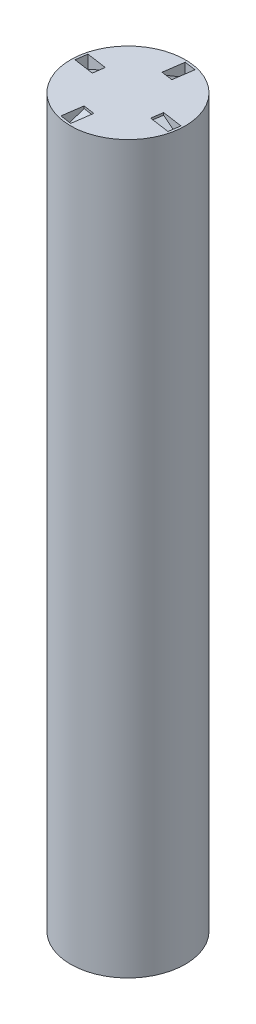
SolidWorks part; units mm, degrees
ref_plane "Front Plane" through (0, 0, 0) normal (0, 0, 1) x (1, 0, 0)
ref_plane "Top Plane" through (0, 0, 0) normal (0, 1, 0) x (1, 0, 0)
ref_plane "Right Plane" through (0, 0, 0) normal (1, 0, 0) x (0, 0, -1)
sketch "Sketch1" plane through (0, 0, 0) normal (0, 1, 0) x (1, 0, 0)
  circle A0 centre (0, 0) radius 6.395
  dimension "D1" = 12.79
extrude "Boss-Extrude1" add sketch "Sketch1" along normal blind 80.99
sketch "Sketch2" [suppressed] plane through (0, 0, 0) normal (0, -1, 0) x (1, 0, 0)
  line L1 (-3.07, -1.85) -> (3.07, -1.85)
  line L2 (-3.07, -1.85) -> (-3.07, 1.85)
  line L3 (-3.07, 1.85) -> (3.07, 1.85)
  line L4 (3.07, -1.85) -> (3.07, 1.85)
  line L5 (-3.07, -1.85) -> (3.07, 1.85) construction
  line L6 (-3.07, 1.85) -> (3.07, -1.85) construction
  point P0 (0, 0)
  dimension "D1" = 6.14
  dimension "D2" = 3.7
sketch "Sketch3" plane through (0, 0, 0) normal (0, -1, 0) x (1, 0, 0)
  line L1 (-3.07, -1.85) -> (3.07, -1.85)
  line L2 (-3.07, -1.85) -> (-3.07, 1.85)
  line L3 (-3.07, 1.85) -> (3.07, 1.85)
  line L4 (3.07, -1.85) -> (3.07, 1.85)
  line L5 (-3.07, -1.85) -> (3.07, 1.85) construction
  line L6 (-3.07, 1.85) -> (3.07, -1.85) construction
  point P0 (0, 0)
  dimension "D1" = 6.14
  dimension "D2" = 3.7
extrude "Cut-Extrude2" cut sketch "Sketch3" against normal blind 8.5
sketch "Sketch4" plane through (-0.0913, 0, 0.6335) normal (-0.1426, 0, 0.9898) x (0.9898, 0, 0.1426)
  line L0 (-3.841, 80.99) -> (-6.121, 80.99)
  line L1 (6.395, 80.99) -> (-6.395, 80.99) construction
  line L2 (-3.841, 80.7337) -> (-3.841, 81.9237) construction
  line L3 (-6.121, 79.5137) -> (-6.121, 81.9237) construction
  line L4 (-6.121, 80.99) -> (-6.121, 79.5137)
  line L5 (-6.121, 79.5137) -> (-3.841, 80.7337)
  line L6 (-3.841, 80.7337) -> (-3.841, 80.99)
  dimension "D1" = 0.2563
  dimension "D2" = 2.28
  dimension "D3" = 1.4763
extrude "Cut-Extrude3" cut sketch "Sketch4" against normal blind 1.28
pattern_circular "CirPattern1" count 4 over 360 about axis through (0, 0, 0) along (0, 1, 0) of "Cut-Extrude3"
sketch "Sketch5" plane through (0, 80.99, 0) normal (0, 1, 0) x (1, 0, 0)
